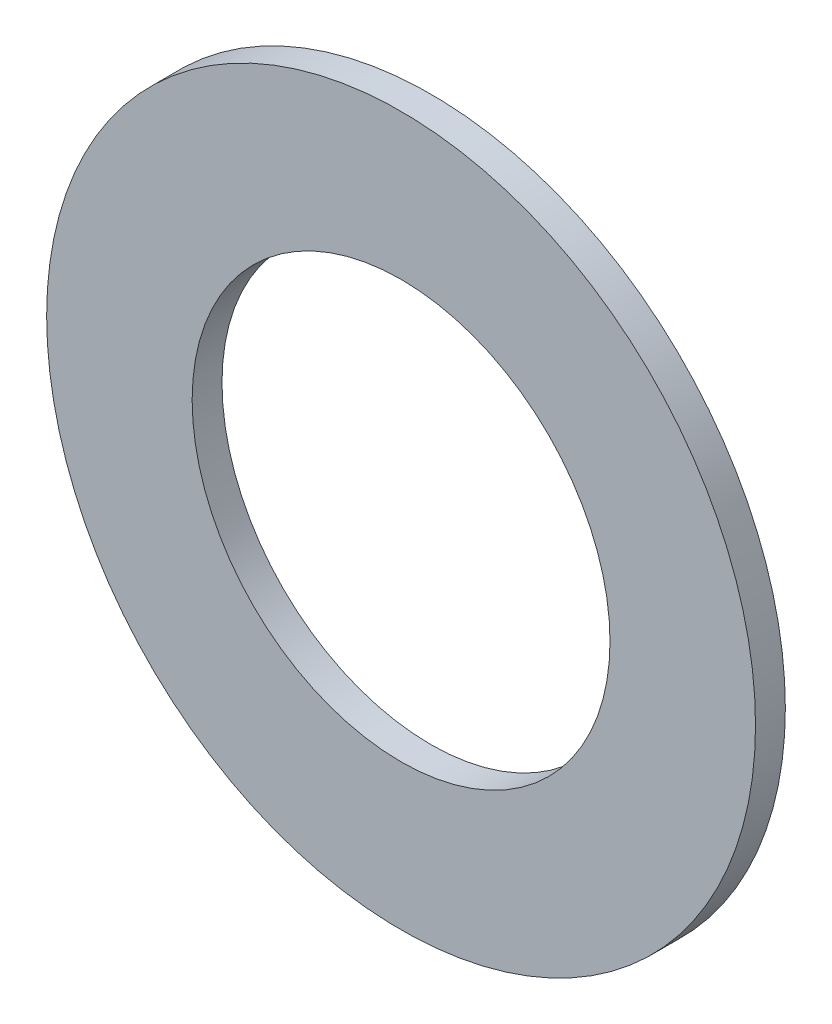
SolidWorks part; units mm, degrees
ref_plane "FRONT" through (0, 0, 0) normal (0, 0, 1) x (1, 0, 0)
ref_plane "TOP" through (0, 0, 0) normal (0, 1, 0) x (1, 0, 0)
ref_plane "SIDE" through (0, 0, 0) normal (1, 0, 0) x (0, 0, -1)
sketch "Sketch1" plane through (0, 0, 0) normal (0, 0, 1) x (1, 0, 0)
  circle A0 centre (0, 0) radius 3.556 construction
  circle A1 centre (0, 0) radius 3.556
  circle A2 centre (0, 0) radius 6.0325
  dimension "D1" = 12.065
extrude "Base-Extrude" add sketch "Sketch1" along normal blind 0.508
